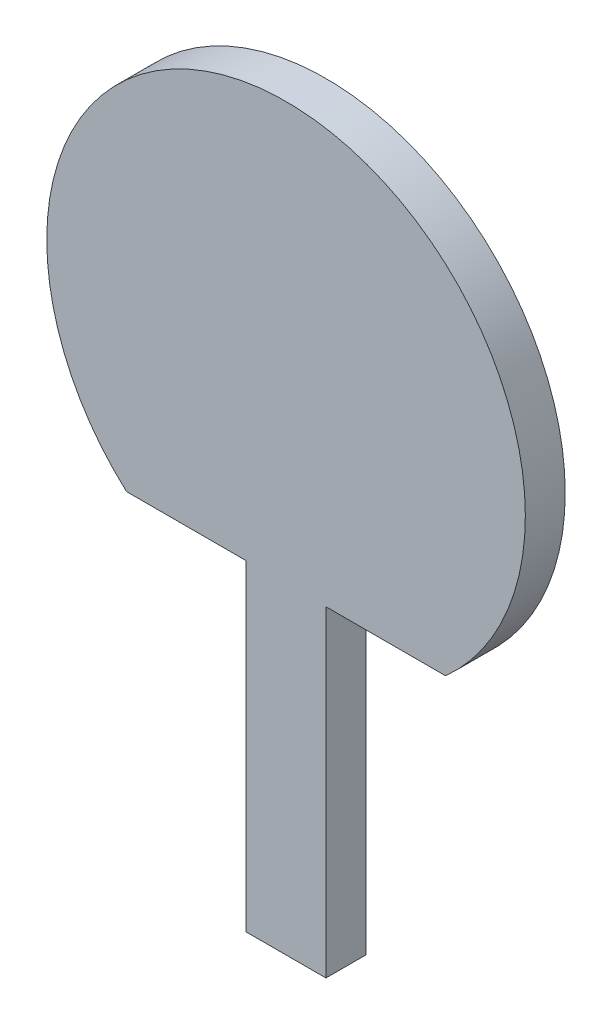
SolidWorks part; units mm, degrees
ref_plane "Front Plane" through (0, 0, 0) normal (0, 0, 1) x (1, 0, 0)
ref_plane "Top Plane" through (0, 0, 0) normal (0, 1, 0) x (1, 0, 0)
ref_plane "Right Plane" through (0, 0, 0) normal (1, 0, 0) x (0, 0, -1)
sketch "Sketch1" plane through (0, 0, 0) normal (0, 0, 1) x (1, 0, 0)
  line L0 (-40, -44.7214) -> (-10, -44.7214)
  line L1 (0, 0) -> (120.6566, 0) construction
  line L2 (0, -44.7214) -> (0, -195.4098) construction
  line L3 (10, -44.7214) -> (40, -44.7214)
  line L4 (-10, -125.3402) -> (10, -125.3402)
  line L5 (-10, -125.3402) -> (-10, -44.7214)
  line L7 (10, -125.3402) -> (10, -44.7214)
  line L8 (-10, -125.3402) -> (10, -44.7214) construction
  line L9 (-10, -44.7214) -> (10, -125.3402) construction
  arc A1 (40, -44.7214) -> (-40, -44.7214) centre (0, 0) ccw
  point P8 (0, -85.0308)
  dimension "D1" = 80
  dimension "D3" = 20
extrude "Boss-Extrude1" add sketch "Sketch1" along normal blind 10
ref_plane "Plane1" through (0, -44.7214, 0) normal (0, -1, 0) x (-1, 0, 0)
sketch3d "3DSketch1"
  line L0 (-10, -125.3402, 5) -> (10, -125.3402, 5) construction
  line L1 (-10, -125.3402, 10) -> (-10, -125.3402, 0) construction
  line L2 (10, -125.3402, 10) -> (10, -125.3402, 0) construction
  line L3 (0, -125.3402, 10) -> (0, -125.3402, 0) construction
  line L4 (-10, -125.3402, 10) -> (10, -125.3402, 10) construction
  line L5 (-10, -125.3402, 0) -> (10, -125.3402, 0) construction
sketch3d "3DSketch2"
  line L0 (-10, -125.3402, 5) -> (10, -125.3402, 5) construction
  point P0 (0, -125.3402, 5)
